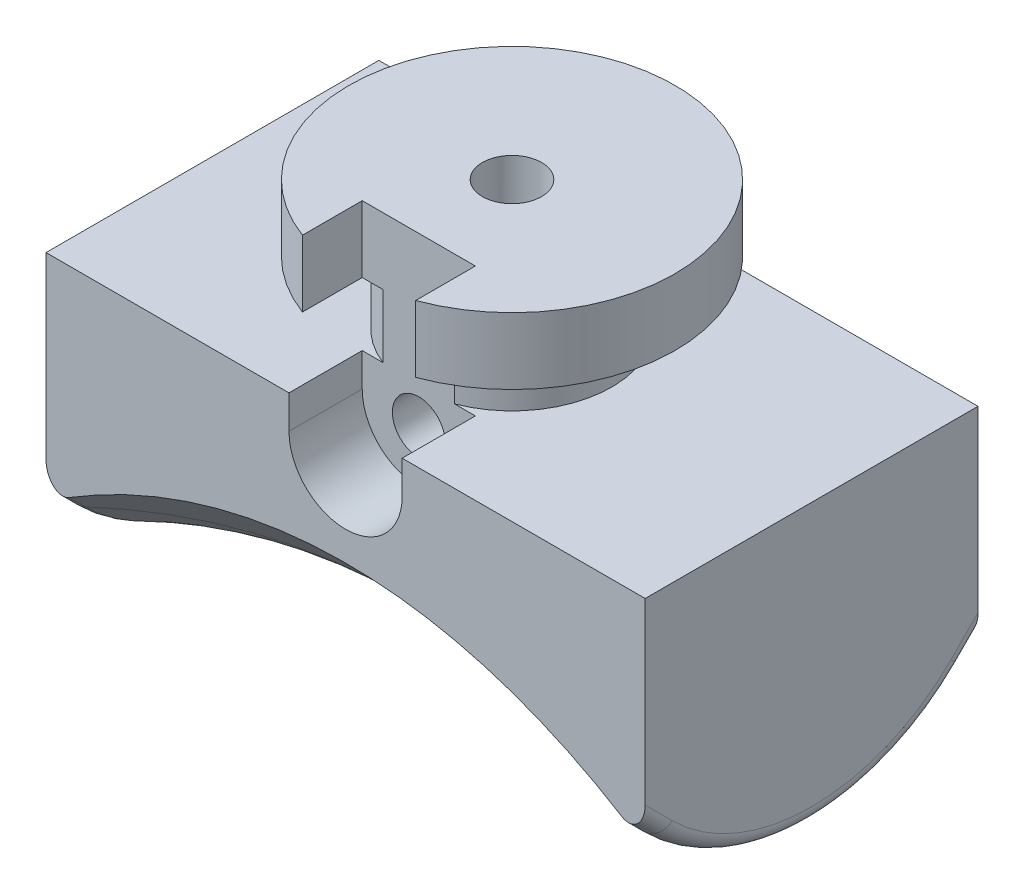
SolidWorks part; units mm, degrees
material "6061-T6 (SS)"
ref_plane "Front Plane" through (0, 0, 0) normal (0, 0, 1) x (1, 0, 0)
ref_plane "Top Plane" through (0, 0, 0) normal (0, 1, 0) x (1, 0, 0)
ref_plane "Right Plane" through (0, 0, 0) normal (1, 0, 0) x (0, 0, -1)
sketch "Sketch1" plane through (0, 0, 0) normal (1, 0, 0) x (0, 0, -1)
  line L0 (3.0052, -3.0052) -> (20, 13.9896)
  line L1 (0, 30) -> (20, 30)
  line L2 (0, 0) -> (0, -4.25) construction
  line L3 (0, 0) -> (2.9486, 0) construction
  line L4 (3.0052, 8.9031) -> (3.0052, -10.7555) construction
  line L5 (20, 30) -> (20, 13.9896)
  line L6 (0, 30) -> (0, -4.25)
  arc A0 (0, -4.25) -> (3.0052, -3.0052) centre (0, 0) ccw
  point P14 (0, 30)
  dimension "D1" = 8.5
  dimension "D2" = 30
  dimension "D3" = 45
  dimension "D4" = 20
extrude "Boss-Extrude1" add sketch "Sketch1" along normal mid plane 18
sketch "Sketch2" plane through (0, 0, 0) normal (1, 0, 0) x (0, 0, -1)
  line L0 (3.0052, -3.0052) -> (20, 13.9896) construction
  line L1 (3.0052, -3.0052) -> (20, 13.9896)
  arc A0 (0, -4.25) -> (3.0052, -3.0052) centre (0, 0) ccw construction
  arc A1 (0, -4.25) -> (3.0052, -3.0052) centre (0, 0) ccw
sketch "Sketch3" plane through (0, 0, 0) normal (0, 0, 1) x (1, 0, 0)
  line L0 (9, -4.25) -> (-9, -4.25) construction
  line L1 (9, -4.25) -> (-9, -4.25)
  line L2 (0, 0) -> (0, 23.6164) construction
  line L3 (-11.3012, -4.65) -> (15.1743, -4.65) construction
  line L4 (-9, -4.25) -> (-9, -6.7012)
  line L5 (9, -4.25) -> (9, -6.7012)
  line L6 (-9, 30) -> (-9, -4.25) construction
  arc A0 (9, -6.7012) -> (-9, -6.7012) centre (0, -25.42) ccw
  dimension "D1" = 41.54
  dimension "D2" = 0.4
sweep "Sweep1" add profiles "Sketch3" path "Sketch2"
sketch "Sketch4" plane through (0, 0, -20) normal (0, 0, -1) x (-1, 0, 0)
  line L0 (9, 13.9896) -> (9, 30) construction
  line L1 (-9, 30) -> (9, 30)
  line L2 (-9, 30) -> (-9, -14.3136)
  line L3 (-9, -14.3136) -> (9, -14.3136)
  line L4 (9, 30) -> (9, -14.3136)
extrude "Cut-Extrude3" cut sketch "Sketch4" along normal blind 6
fillet "Fillet1" radius 0.5 4 edges at (9, 2.8923, -12.3692) (-9, 2.8923, -12.3692) (9, -6.1911, -2.5644) (-9, -6.1911, -2.5644)
mirror "Mirror1" about plane through (9, 30, 0) normal (0, 0, -1) of bodies 103
sketch "Sketch5" plane through (0, 0, 0) normal (1, 0, 0) x (0, 0, -1)
  line L0 (20, 16) -> (-7.4856, 10.6573)
  line L1 (-11.2454, 30) -> (20, 30)
  line L2 (20, 30) -> (20, 16)
  line L3 (20, 11.6247) -> (20, 30) construction
  line L4 (20, 30) -> (-20, 30) construction
  line L5 (-11.2454, 30) -> (-7.4856, 10.6573)
  dimension "D1" = 14
  dimension "D2" = 11
  dimension "D3" = 28
extrude "Cut-Extrude4" cut sketch "Sketch5" against normal mid plane 40
sketch "Sketch8" plane through (-9, 0, 0) normal (-1, 0, 0) x (0, 0, 1)
  line L0 (10.6659, 27.019) -> (20, 28)
  line L1 (11.2454, 30) -> (7.4856, 10.6573) construction
  line L2 (20, 11.6247) -> (20, 30) construction
  line L3 (20, 28) -> (20, 30)
  line L4 (20, 30) -> (11.2454, 30)
  line L5 (11.2454, 30) -> (10.6659, 27.019)
  dimension "D1" = 2
  dimension "D2" = 6
extrude "Cut-Extrude5" cut sketch "Sketch8" against normal through all
sketch "Sketch10" plane through (-9, 0, 0) normal (-1, 0, 0) x (0, 0, 1)
  line L0 (20, 28) -> (29.9452, 29.0453)
  line L1 (29.9452, 29.0453) -> (30.2588, 26.0617)
  line L2 (30.2588, 26.0617) -> (20, 24.9835)
  line L3 (20, 11.6247) -> (20, 28) construction
  line L4 (20, 28) -> (20, 24.9835)
  line L5 (10.6659, 27.019) -> (20, 28) construction
  dimension "D1" = 3
  dimension "D2" = 10
extrude "Boss-Extrude2" add sketch "Sketch10" against normal up to surface (18 mm away) up to face at (9, 11.852, 2.2689)
fillet "Fillet2" radius 3 4 edges at (0, 10.6573, 7.4856)
sketch "Sketch11" plane through (-9, 0, 0) normal (-1, 0, 0) x (0, 0, 1)
  line L0 (0, 0) -> (0, -17.5541) construction
  line L1 (-5, 2) -> (5, 2)
  line L2 (-5, 2) -> (-5, -18)
  line L3 (-5, -18) -> (5, -18)
  line L4 (5, 2) -> (5, -18)
  line L5 (-5, 2) -> (5, -18) construction
  line L6 (-5, -18) -> (5, 2) construction
  line L7 (0, 0) -> (23.2661, 0) construction
  point P0 (0, -8)
  dimension "D1" = 10
  dimension "D2" = 2
  dimension "D3" = 20
extrude "Cut-Extrude6" cut sketch "Sketch11" against normal through all flip side to cut
sketch "Sketch13" plane through (0, 0, 0) normal (1, 0, 0) x (0, 0, -1)
  line L0 (0, 2) -> (0, 5.9)
  line L1 (0, 5.9) -> (-4.9, 5.9)
  line L2 (-4.9, 5.9) -> (-4.9, 3.9)
  line L3 (-4.9, 3.9) -> (-3, 3.9)
  line L4 (-3, 3.9) -> (-3, 2)
  line L5 (0, 2) -> (-3, 2)
  line L6 (0, 0) -> (0, -2.6273) construction
  line L7 (-5, 2) -> (5, 2) construction
  dimension "D1" = 6
  dimension "D2" = 1.9
  dimension "D3" = 2
  dimension "D4" = 1.9
revolve "Revolve1" add sketch "Sketch13" angle 360 about L6
hole_wizard "#2-56 Tapped Hole1" positions "Sketch15" profile "Sketch14" tap size "#2-56" standard "ANSI Inch"
sketch "Sketch15" plane through (0, 5.9, 0) normal (0, 1, 0) x (1, 0, 0)
  circle A0 centre (0, 0) radius 4.9 construction
  point P0 (0, 0)
sketch "Sketch14" plane through (0, 5.9, 0) normal (1, 0, 0) x (0, 0, 1)
  line L0 (0, 0) -> (0, 6.2642)
  line L1 (0, 6.2642) -> (0.889, 5.73)
  line L2 (0.889, 5.73) -> (0.889, 0)
  line L5 (0.889, 0) -> (0, 0)
  line L10 (0, 6.2642) -> (-0.889, 5.73) construction
  line L11 (0, -6.35) -> (0, 107.95) construction
  dimension "Tap Drill Dia." = 1.778
  dimension "Tap Drill Depth" = 5.73
  dimension "Drill Angle" = 118
cosmetic thread "Hole Thread1" parameters "D1"=4.37, "D2"=2.1844
sketch "Sketch16" plane through (0, 0, 5) normal (0, 0, 1) x (1, 0, 0)
  line L0 (0, 7.9613) -> (0, 1) construction
  line L1 (1.7, 7.9613) -> (1.7, 1)
  line L2 (-1.7, 7.9613) -> (-1.7, 1)
  line L3 (9, 2) -> (-9, 2) construction
  arc A0 (1.7, 7.9613) -> (-1.7, 7.9613) centre (0, 7.9613) ccw
  arc A1 (-1.7, 1) -> (1.7, 1) centre (0, 1) ccw
  point P2 (0, 4.4806)
  dimension "D1" = 3.4
  dimension "D2" = 1
  dimension "D3" = 6.9613
extrude "Cut-Extrude7" cut sketch "Sketch16" against normal blind 2.2
hole_wizard "1/16 (0.0625) Diameter Hole1" positions "Sketch18" profile "Sketch17" hole size "1/16" standard "ANSI Inch" end condition through all
sketch "Sketch18" plane through (0, 0, 2.8) normal (0, 0, 1) x (1, 0, 0)
  point P0 (0, 0.8533)
sketch "Sketch17" plane through (0, 0.8533, 2.8) normal (1, 0, 0) x (0, -1, 0)
  line L0 (0, 0) -> (0, 7.8)
  line L1 (0, 7.8) -> (0.7937, 7.8)
  line L2 (0.7937, 7.8) -> (0.7937, 0)
  line L5 (0.7937, 0) -> (0, 0)
  line L11 (0, -6.35) -> (0, 107.95) construction
  dimension "Thru Hole Dia." = 1.5875
  dimension "Thru Hole Depth" = 7.8
